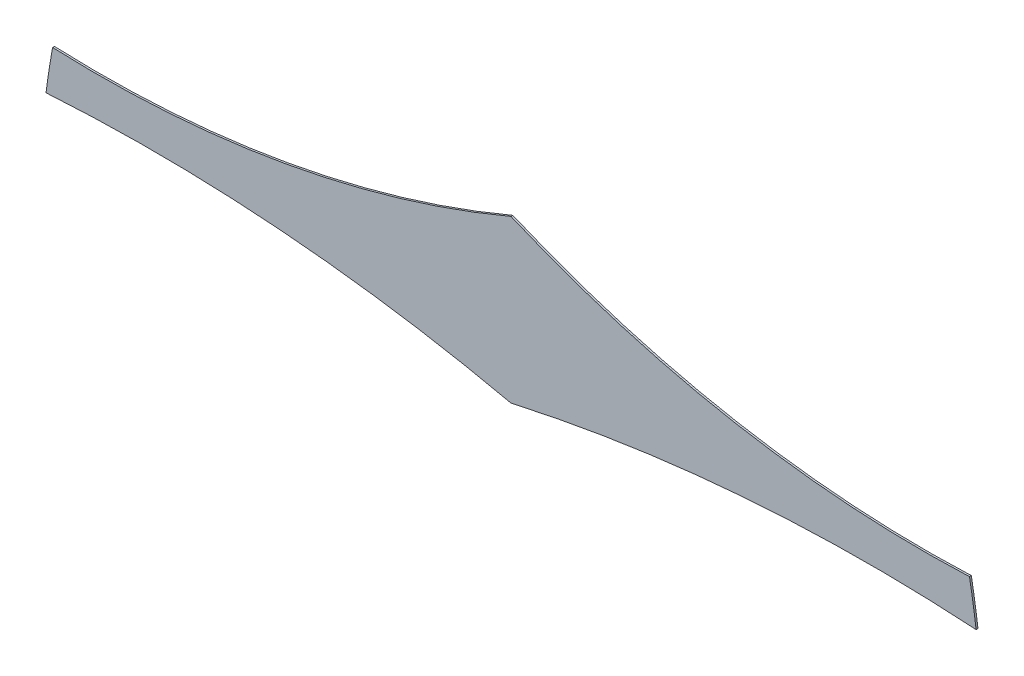
SolidWorks part; units mm, degrees
ref_plane "Alzado" through (0, 0, 0) normal (0, 0, 1) x (1, 0, 0)
ref_plane "Planta" through (0, 0, 0) normal (0, 1, 0) x (1, 0, 0)
ref_plane "Vista lateral" through (0, 0, 0) normal (1, 0, 0) x (0, 0, -1)
sketch "Model" plane through (0, 0, 0) normal (0, 0, 1) x (1, 0, 0)
  arc A0 (60.636, 28.8512) -> (60.2798, 31.1244) centre (14.8173, 22.8356) ccw
  arc A1 (11.322, 31.1159) -> (10.97, 28.8428) centre (56.7986, 22.9099) ccw
  arc A2 (11.322, 31.1159) -> (35.7981, 35.5401) centre (13.7564, 87.5647) ccw
  arc A3 (35.7981, 35.5401) -> (60.2798, 31.1244) centre (57.8237, 87.5816) ccw
  arc A4 (60.636, 28.8512) -> (35.8002, 26.9087) centre (55.0169, -59.0454) ccw
  arc A5 (35.8002, 26.9087) -> (10.9666, 28.8426) centre (16.6148, -59.0421) ccw
extrude "Saliente-Extruir1" add sketch "Model" along normal blind 0.1 contours A5 A4 A0 A3 A2 A1
